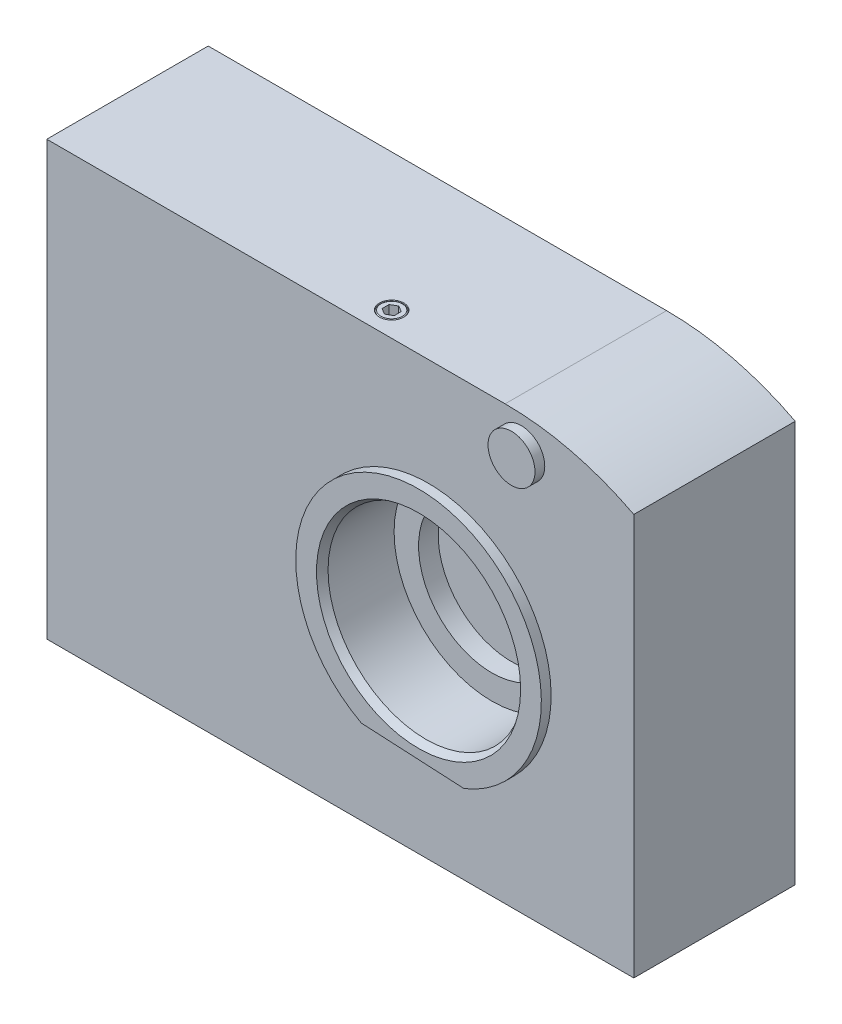
SolidWorks part; units mm, degrees
material "201.0-T43 Insulated Mold Casting (SS)"
ref_plane "Front Plane" through (0, 0, 0) normal (0, 0, 1) x (1, 0, 0)
ref_plane "Top Plane" through (0, 0, 0) normal (0, 1, 0) x (1, 0, 0)
ref_plane "Right Plane" through (0, 0, 0) normal (1, 0, 0) x (0, 0, -1)
ref_plane "Plane1" through (0, 0, 0) normal (0, 0, 1) x (1, 0, 0)
sketch "Sketch1" plane through (0, 0, 0) normal (0, 0, 1) x (1, 0, 0)
  line L0 (0, 0) -> (120, 0)
  line L1 (120, 0) -> (120, 82.0699)
  line L2 (93.7, 88.5) -> (0, 88.5)
  line L3 (0, 88.5) -> (0, 0)
  arc A0 (120, 82.0699) -> (93.7, 88.5) centre (93.7, 31.5) ccw
extrude "Boss-Extrude1" add sketch "Sketch1" against normal blind 33
ref_plane "Plane2" through (0, 0, 0) normal (0, 0, 1) x (1, 0, 0)
sketch "Sketch2" plane through (0, 0, 0) normal (0, 0, 1) x (1, 0, 0)
  line L0 (66.3249, 19.2806) -> (87.2885, 18.1819)
  arc A0 (87.2885, 18.1819) -> (66.3249, 19.2806) centre (78, 41.5) ccw
extrude "Boss-Extrude2" add sketch "Sketch2" along normal blind 2
ref_plane "Plane3" through (78, 0, 0) normal (1, 0, 0) x (0, 0, -1)
sketch "Sketch3" plane through (78, 0, 0) normal (1, 0, 0) x (0, 0, -1)
  line L0 (-2, 41.5) -> (-2, 62.366)
  line L1 (-2, 62.366) -> (-0.5, 61.5)
  line L2 (-0.5, 61.5) -> (13, 61.5)
  line L3 (13, 61.5) -> (13, 56.5)
  line L4 (13, 56.5) -> (17, 56.5)
  line L5 (17, 56.5) -> (17, 61.5)
  line L6 (17, 61.5) -> (28.5, 61.5)
  line L7 (28.5, 61.5) -> (30, 62.366)
  line L8 (30, 62.366) -> (30, 72.5)
  line L9 (30, 72.5) -> (33, 72.5)
  line L10 (33, 72.5) -> (33, 41.5)
  line L11 (33, 41.5) -> (-2, 41.5)
  line L12 (33, 41.5) -> (-2, 41.5) construction
revolve "Cut-Revolve1" cut sketch "Sketch3" angle 360 about L12
ref_plane "Plane4" through (19.5, 0, 0) normal (1, 0, 0) x (0, 0, -1)
sketch "Sketch4" plane through (19.5, 0, 0) normal (1, 0, 0) x (0, 0, -1)
  line L0 (23.7, 8) -> (26.7, 11)
  line L1 (26.7, 11) -> (26.7, 12.4)
  line L2 (26.7, 12.4) -> (26.1, 13)
  line L3 (26.1, 13) -> (20.7, 13)
  line L4 (20.7, 13) -> (20.7, 13.5)
  line L5 (20.7, 13.5) -> (33, 13.5)
  line L6 (33, 13.5) -> (33, 8)
  line L7 (33, 8) -> (23.7, 8)
  line L8 (33, 8) -> (23.7, 8) construction
revolve "Cut-Revolve2" cut sketch "Sketch4" angle 360 about L8
ref_plane "Plane5" through (103.5, 0, 0) normal (1, 0, 0) x (0, 0, -1)
sketch "Sketch5" plane through (103.5, 0, 0) normal (1, 0, 0) x (0, 0, -1)
  line L0 (23.7, 6.5) -> (26.7, 9.5)
  line L1 (26.7, 9.5) -> (26.7, 10.9)
  line L2 (26.7, 10.9) -> (26.1, 11.5)
  line L3 (26.1, 11.5) -> (20.7, 11.5)
  line L4 (20.7, 11.5) -> (20.7, 12)
  line L5 (20.7, 12) -> (33, 12)
  line L6 (33, 12) -> (33, 6.5)
  line L7 (33, 6.5) -> (23.7, 6.5)
  line L8 (33, 6.5) -> (23.7, 6.5) construction
revolve "Cut-Revolve3" cut sketch "Sketch5" angle 360 about L8
ref_plane "Plane6" through (11.5, 0, 0) normal (1, 0, 0) x (0, 0, -1)
sketch "Sketch6" plane through (11.5, 0, 0) normal (1, 0, 0) x (0, 0, -1)
  line L0 (23.7, 58) -> (26.7, 61)
  line L1 (26.7, 61) -> (26.7, 62.4)
  line L2 (26.7, 62.4) -> (26.1, 63)
  line L3 (26.1, 63) -> (20.7, 63)
  line L4 (20.7, 63) -> (20.7, 63.5)
  line L5 (20.7, 63.5) -> (33, 63.5)
  line L6 (33, 63.5) -> (33, 58)
  line L7 (33, 58) -> (23.7, 58)
  line L8 (33, 58) -> (23.7, 58) construction
revolve "Cut-Revolve4" cut sketch "Sketch6" angle 360 about L8
ref_plane "Plane7" through (107, 0, 0) normal (1, 0, 0) x (0, 0, -1)
sketch "Sketch7" plane through (107, 0, 0) normal (1, 0, 0) x (0, 0, -1)
  line L0 (23.7, 49) -> (26.7, 52)
  line L1 (26.7, 52) -> (26.7, 53.4)
  line L2 (26.7, 53.4) -> (26.1, 54)
  line L3 (26.1, 54) -> (20.7, 54)
  line L4 (20.7, 54) -> (20.7, 54.5)
  line L5 (20.7, 54.5) -> (33, 54.5)
  line L6 (33, 54.5) -> (33, 49)
  line L7 (33, 49) -> (23.7, 49)
  line L8 (33, 49) -> (23.7, 49) construction
revolve "Cut-Revolve5" cut sketch "Sketch7" angle 360 about L8
ref_plane "Plane8" through (0, 0, -33) normal (0, 0, 1) x (1, 0, 0)
sketch "Sketch8" plane through (0, 0, -33) normal (0, 0, 1) x (1, 0, 0)
  line L0 (17, 9.4434) -> (17, 6.5566)
  line L1 (17, 6.5566) -> (19.5, 5.1132)
  line L2 (19.5, 5.1132) -> (22, 6.5566)
  line L3 (22, 6.5566) -> (22, 9.4434)
  line L4 (22, 9.4434) -> (19.5, 10.8868)
  line L5 (19.5, 10.8868) -> (17, 9.4434)
extrude "Cut-Extrude1" cut sketch "Sketch8" along normal blind 9.3
ref_plane "Plane9" through (0, 0, -33) normal (0, 0, 1) x (1, 0, 0)
sketch "Sketch9" plane through (0, 0, -33) normal (0, 0, 1) x (1, 0, 0)
  line L0 (101, 7.9434) -> (101, 5.0566)
  line L1 (101, 5.0566) -> (103.5, 3.6132)
  line L2 (103.5, 3.6132) -> (106, 5.0566)
  line L3 (106, 5.0566) -> (106, 7.9434)
  line L4 (106, 7.9434) -> (103.5, 9.3868)
  line L5 (103.5, 9.3868) -> (101, 7.9434)
extrude "Cut-Extrude2" cut sketch "Sketch9" along normal blind 9.3
ref_plane "Plane10" through (0, 0, -33) normal (0, 0, 1) x (1, 0, 0)
sketch "Sketch10" plane through (0, 0, -33) normal (0, 0, 1) x (1, 0, 0)
  line L0 (9, 59.4434) -> (9, 56.5566)
  line L1 (9, 56.5566) -> (11.5, 55.1132)
  line L2 (11.5, 55.1132) -> (14, 56.5566)
  line L3 (14, 56.5566) -> (14, 59.4434)
  line L4 (14, 59.4434) -> (11.5, 60.8868)
  line L5 (11.5, 60.8868) -> (9, 59.4434)
extrude "Cut-Extrude3" cut sketch "Sketch10" along normal blind 9.3
ref_plane "Plane11" through (0, 0, -33) normal (0, 0, 1) x (1, 0, 0)
sketch "Sketch11" plane through (0, 0, -33) normal (0, 0, 1) x (1, 0, 0)
  line L0 (104.5, 50.4434) -> (104.5, 47.5566)
  line L1 (104.5, 47.5566) -> (107, 46.1132)
  line L2 (107, 46.1132) -> (109.5, 47.5566)
  line L3 (109.5, 47.5566) -> (109.5, 50.4434)
  line L4 (109.5, 50.4434) -> (107, 51.8868)
  line L5 (107, 51.8868) -> (104.5, 50.4434)
extrude "Cut-Extrude4" cut sketch "Sketch11" along normal blind 9.3
ref_plane "Plane12" through (0, 14.5, 0) normal (0, 1, 0) x (1, 0, 0)
sketch "Sketch12" plane through (0, 14.5, 0) normal (0, 1, 0) x (1, 0, 0)
  line L0 (46, 11.4806) -> (43.5415, 12.9)
  line L1 (43.5415, 12.9) -> (43.5415, 32.4585)
  line L2 (43.5415, 32.4585) -> (43, 33)
  line L3 (43, 33) -> (46, 33)
  line L4 (46, 33) -> (46, 11.4806)
  line L5 (46, 33) -> (46, 11.4806) construction
revolve "Cut-Revolve6" cut sketch "Sketch12" angle 360 about L5
ref_plane "Plane13" through (0, 14.5, 0) normal (0, 1, 0) x (1, 0, 0)
sketch "Sketch13" plane through (0, 14.5, 0) normal (0, 1, 0) x (1, 0, 0)
  line L0 (110, 11.4806) -> (107.5415, 12.9)
  line L1 (107.5415, 12.9) -> (107.5415, 32.4585)
  line L2 (107.5415, 32.4585) -> (107, 33)
  line L3 (107, 33) -> (110, 33)
  line L4 (110, 33) -> (110, 11.4806)
  line L5 (110, 33) -> (110, 11.4806) construction
revolve "Cut-Revolve7" cut sketch "Sketch13" angle 360 about L5
ref_plane "Plane14" through (0, 68.5, 0) normal (0, 1, 0) x (1, 0, 0)
sketch "Sketch14" plane through (0, 68.5, 0) normal (0, 1, 0) x (1, 0, 0)
  line L0 (46, 11.4806) -> (43.5415, 12.9)
  line L1 (43.5415, 12.9) -> (43.5415, 32.4585)
  line L2 (43.5415, 32.4585) -> (43, 33)
  line L3 (43, 33) -> (46, 33)
  line L4 (46, 33) -> (46, 11.4806)
  line L5 (46, 33) -> (46, 11.4806) construction
revolve "Cut-Revolve8" cut sketch "Sketch14" angle 360 about L5
ref_plane "Plane15" through (0, 68.5, 0) normal (0, 1, 0) x (1, 0, 0)
sketch "Sketch15" plane through (0, 68.5, 0) normal (0, 1, 0) x (1, 0, 0)
  line L0 (110, 11.4806) -> (107.5415, 12.9)
  line L1 (107.5415, 12.9) -> (107.5415, 32.4585)
  line L2 (107.5415, 32.4585) -> (107, 33)
  line L3 (107, 33) -> (110, 33)
  line L4 (110, 33) -> (110, 11.4806)
  line L5 (110, 33) -> (110, 11.4806) construction
revolve "Cut-Revolve9" cut sketch "Sketch15" angle 360 about L5
ref_plane "Plane16" through (0, 0, 0) normal (0, 0, 1) x (1, 0, 0)
sketch "Sketch16" plane through (0, 0, 0) normal (0, 0, 1) x (1, 0, 0)
  circle A0 centre (97, 81.5) radius 4.8
extrude "Boss-Extrude3" add sketch "Sketch16" along normal blind 2
ref_plane "Plane17" through (65.5, 0, 0) normal (1, 0, 0) x (0, 0, -1)
sketch "Sketch17" plane through (65.5, 0, 0) normal (1, 0, 0) x (0, 0, -1)
  line L0 (5, 88.5) -> (2.8066, 88.5)
  line L1 (2.8066, 88.5) -> (2.6122, 88.3878)
  line L2 (2.6122, 88.3878) -> (2.5, 88.5)
  line L3 (2.5, 88.5) -> (2.5, 89.5)
  line L4 (2.5, 89.5) -> (5, 89.5)
  line L5 (5, 89.5) -> (5, 88.5)
  line L6 (5, 89.5) -> (5, 88.5) construction
revolve "Cut-Revolve10" cut sketch "Sketch17" angle 360 about L6
ref_plane "Plane18" through (78, 0, 0) normal (1, 0, 0) x (0, 0, -1)
sketch "Sketch18" plane through (78, 0, 0) normal (1, 0, 0) x (0, 0, -1)
  line L0 (17, 41.5) -> (17, 61.5)
  line L1 (17, 61.5) -> (30, 61.5)
  line L2 (30, 61.5) -> (30, 55.5)
  line L3 (30, 55.5) -> (38, 55.5)
  line L4 (38, 55.5) -> (41, 52.5)
  line L5 (41, 52.5) -> (41, 47.5)
  line L6 (41, 47.5) -> (57.5, 47.5)
  line L7 (57.5, 47.5) -> (58.5, 46.5)
  line L8 (58.5, 46.5) -> (58.5, 41.5)
  line L9 (58.5, 41.5) -> (17, 41.5)
  line L10 (58.5, 41.5) -> (17, 41.5) construction
revolve "Revolve1" add sketch "Sketch18" angle 360 about L10
ref_plane "Plane19" through (0, 88.5, 0) normal (0, 1, 0) x (1, 0, 0)
sketch "Sketch19" plane through (0, 88.5, 0) normal (0, 1, 0) x (1, 0, 0)
  line L0 (64.25, 5.7217) -> (64.25, 4.2783)
  line L1 (64.25, 4.2783) -> (65.5, 3.5566)
  line L2 (65.5, 3.5566) -> (66.75, 4.2783)
  line L3 (66.75, 4.2783) -> (66.75, 5.7217)
  line L4 (66.75, 5.7217) -> (65.5, 6.4434)
  line L5 (65.5, 6.4434) -> (64.25, 5.7217)
extrude "Cut-Extrude5" cut sketch "Sketch19" against normal blind 3
